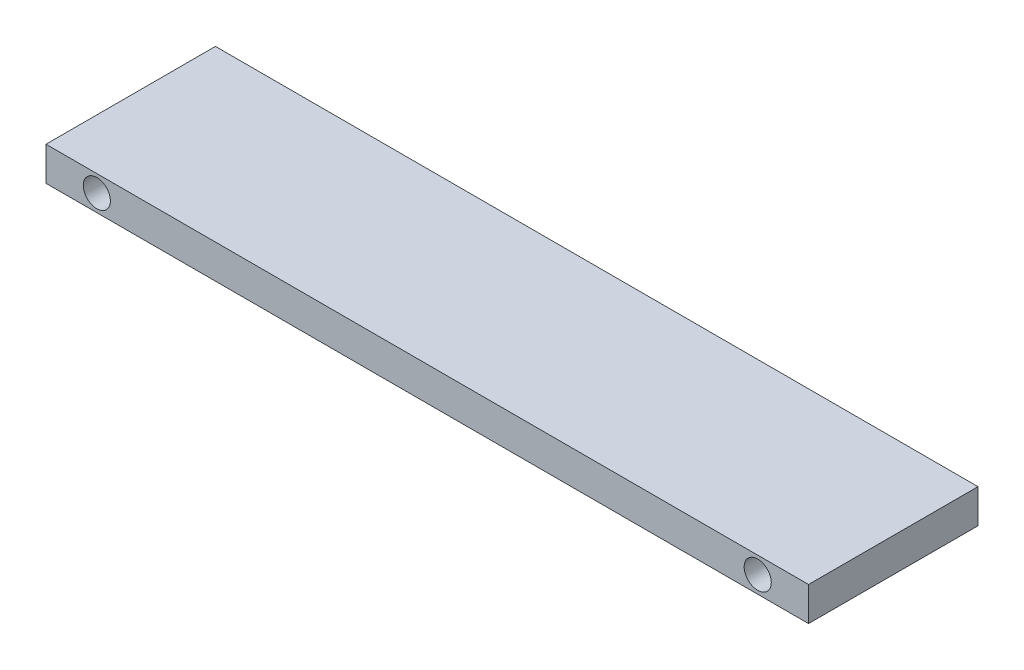
SolidWorks part; units mm, degrees
ref_plane "Front Plane" through (0, 0, 0) normal (0, 0, 1) x (1, 0, 0)
ref_plane "Top Plane" through (0, 0, 0) normal (0, 1, 0) x (1, 0, 0)
ref_plane "Right Plane" through (0, 0, 0) normal (1, 0, 0) x (0, 0, -1)
sketch "Sketch1" plane through (0, 0, 0) normal (0, 1, 0) x (1, 0, 0)
  line L1 (-225, -50) -> (225, -50)
  line L2 (-225, -50) -> (-225, 50)
  line L3 (-225, 50) -> (225, 50)
  line L4 (225, -50) -> (225, 50)
  line L5 (-225, -50) -> (225, 50) construction
  line L6 (-225, 50) -> (225, -50) construction
  point P0 (0, 0)
  dimension "D1" = 450
  dimension "D2" = 100
extrude "Boss-Extrude1" add sketch "Sketch1" along normal blind 20
sketch "Sketch2" plane through (0, 0, 50) normal (0, 0, 1) x (1, 0, 0)
  line L0 (225, 20) -> (225, 0) construction
  line L1 (0, 20) -> (0, 0) construction
  line L2 (-225, 20) -> (225, 20) construction
  circle A0 centre (195, 10) radius 8
  circle A1 centre (-195, 10) radius 8
  point P2 (225, 10)
  dimension "D1" = 0
  dimension "D2" = 195
extrude "Cut-Extrude1" cut sketch "Sketch2" against normal through all
